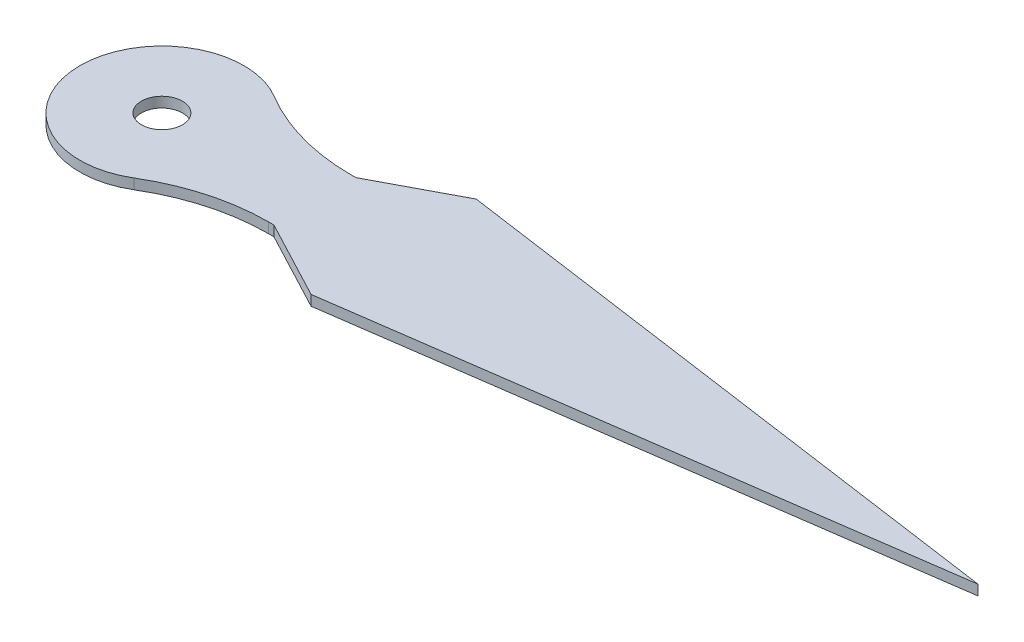
SolidWorks part; units mm, degrees
ref_plane "Front Plane" through (0, 0, 0) normal (0, 0, 1) x (1, 0, 0)
ref_plane "Top Plane" through (0, 0, 0) normal (0, 1, 0) x (1, 0, 0)
ref_plane "Right Plane" through (0, 0, 0) normal (1, 0, 0) x (0, 0, -1)
sketch "Sketch1" plane through (0, 0, 0) normal (0, 1, 0) x (1, 0, 0)
  line L0 (0, 0) -> (39.8018, 0) construction
  line L1 (11.3026, 4.0272) -> (39.8018, 0)
  line L2 (11.3026, -4.0272) -> (39.8018, 0)
  line L3 (3.4641, 2) -> (7.4641, 2)
  line L4 (7.4641, -2) -> (11.3026, -4.0272)
  line L5 (7.4641, 2) -> (11.3026, 4.0272)
  line L6 (3.4641, -2) -> (7.4641, -2)
  circle A0 centre (0, 0) radius 4
  dimension "D3" = 4
extrude "Boss-Extrude2" add sketch "Sketch1" along normal blind 0.5
sketch "Sketch3" plane through (0, 0.5, 0) normal (0, 1, 0) x (1, 0, 0)
  circle A0 centre (0, 0) radius 1
extrude "Cut-Extrude2" cut sketch "Sketch3" against normal through all
fillet "Fillet1" radius 10 2 edges at (3.4641, 0.25, -2) (3.4641, 0.25, 2)
